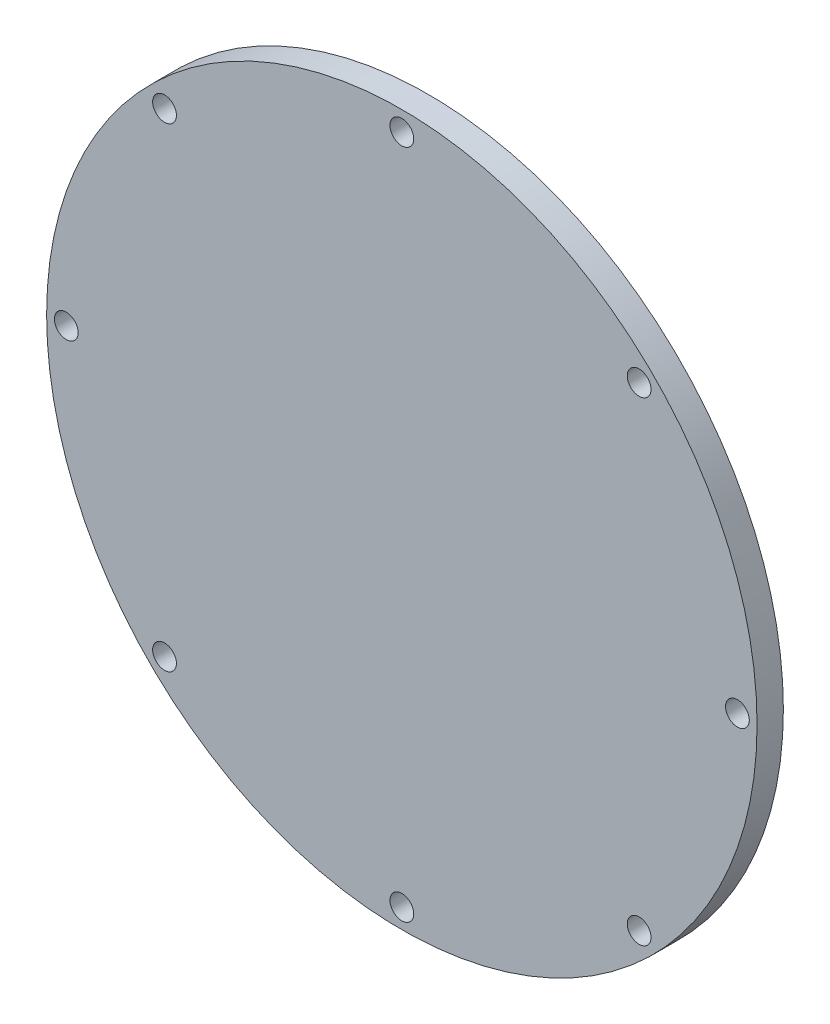
SolidWorks part; units mm, degrees
ref_plane "Front Plane" through (0, 0, 0) normal (0, 0, 1) x (1, 0, 0)
ref_plane "Top Plane" through (0, 0, 0) normal (0, 1, 0) x (1, 0, 0)
ref_plane "Right Plane" through (0, 0, 0) normal (1, 0, 0) x (0, 0, -1)
sketch "Sketch1" plane through (0, 0, 0) normal (0, 0, 1) x (1, 0, 0)
  line L7 (0, -71.3867) -> (50.478, -50.478) construction
  line L8 (50.478, -50.478) -> (71.3867, 0) construction
  line L9 (71.3867, 0) -> (50.478, 50.478) construction
  line L10 (50.478, 50.478) -> (0, 71.3867) construction
  line L11 (0, 71.3867) -> (-50.478, 50.478) construction
  line L12 (-50.478, 50.478) -> (-71.3867, 0) construction
  line L13 (-71.3867, 0) -> (-50.478, -50.478) construction
  line L14 (-50.478, -50.478) -> (0, -71.3867) construction
  circle A0 centre (0, 0) radius 75.565
  circle A1 centre (0, 0) radius 65.9527 construction
  point P15 (50.478, 50.478)
  point P20 (71.3867, 0)
  point P21 (0, 71.3867)
  point P22 (50.478, -50.478)
  point P23 (0, -71.3867)
  point P24 (-50.478, -50.478)
  point P25 (-71.3867, 0)
  point P26 (-50.478, 50.478)
  dimension "D2" = 151.13
  dimension "D1" = 142.7734
extrude "Boss-Extrude1" add sketch "Sketch1" along normal blind 5.6
sketch "Sketch3" plane through (0, 0, 0) normal (0, 0, -1) x (-1, 0, 0)
  point P13 (-50.478, 50.478)
  point P16 (0, 71.3867)
  point P19 (50.478, 50.478)
  point P22 (71.3867, 0)
  point P25 (50.478, -50.478)
  point P28 (0, -71.3867)
  point P31 (-50.478, -50.478)
  point P34 (-71.3867, 0)
hole_wizard "#8 (0.199) Diameter Hole1" positions "Sketch3" profile "Sketch4" hole size "#8" standard "ANSI Inch"
sketch "Sketch4" plane through (50.478, 50.478, 0) normal (1, 0, 0) x (0, 1, 0)
  line L0 (0, 0) -> (0, 10)
  line L1 (0, 10) -> (2.5273, 8.4814)
  line L2 (2.5273, 8.4814) -> (2.5273, 0)
  line L5 (2.5273, 0) -> (0, 0)
  line L10 (0, 10) -> (-2.5273, 8.4814) construction
  line L11 (0, -6.35) -> (0, 107.95) construction
  dimension "Hole Dia." = 5.0546
  dimension "Hole Depth" = 10
  dimension "Drill Angle" = 118
